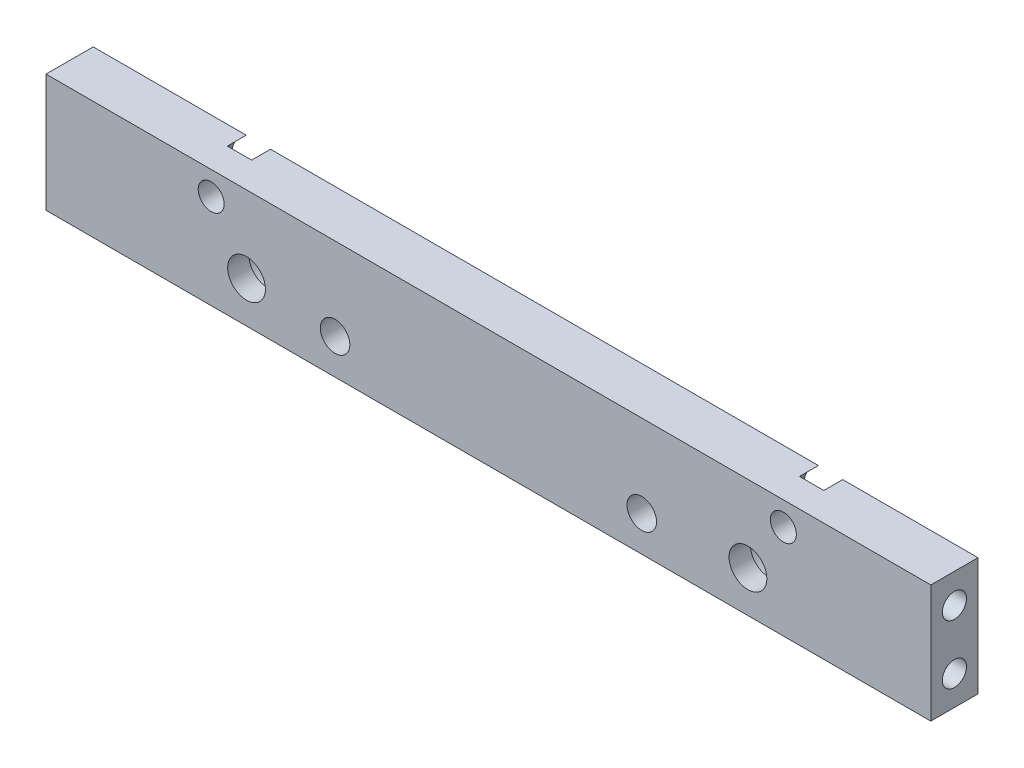
SolidWorks part; units mm, degrees
ref_plane "Front Plane" through (0, 0, 0) normal (0, 0, 1) x (1, 0, 0)
ref_plane "Top Plane" through (0, 0, 0) normal (0, 1, 0) x (1, 0, 0)
ref_plane "Right Plane" through (0, 0, 0) normal (1, 0, 0) x (0, 0, -1)
ref_plane "Plane1" through (0, 0, 4) normal (0, 0, 1) x (1, 0, 0)
sketch "Sketch1" plane through (0, 0, 4) normal (0, 0, 1) x (1, 0, 0)
  line L0 (37.5, -5) -> (37.5, 5)
  line L1 (37.5, 5) -> (-37.5, 5)
  line L2 (-37.5, 5) -> (-37.5, -5)
  line L3 (-37.5, -5) -> (37.5, -5)
extrude "Boss-Extrude1" add sketch "Sketch1" against normal blind 4
hole_wizard "Ø2.5 (2.5) Diameter Hole1" positions "Sketch3" profile "Sketch2" hole size "Ø2.5" standard "ANSI Metric"
sketch "Sketch3" plane through (0, 0, 0) normal (0, 0, -1) x (-1, 0, 0)
  point P0 (-13, -2)
  point P1 (13, -2)
sketch "Sketch2" plane through (13, -2, 0) normal (1, 0, 0) x (0, 1, 0)
  line L0 (0, 0) -> (0, 4)
  line L1 (0, 4) -> (1.25, 4)
  line L2 (1.25, 4) -> (1.25, 0)
  line L5 (1.25, 0) -> (0, 0)
  line L11 (0, -6.35) -> (0, 107.95) construction
  dimension "Thru Hole Dia." = 2.5
  dimension "Thru Hole Depth" = 4
hole_wizard "CBORE for M3 Hex Head Machine Screw1" positions "Sketch5" profile "Sketch4" counterbore size "M3" standard "ANSI Metric"
sketch "Sketch5" plane through (0, 0, 0) normal (0, 0, -1) x (-1, 0, 0)
  point P0 (-22, -1.5)
  point P1 (20.5, -1.5)
sketch "Sketch4" plane through (22, -1.5, 0) normal (1, 0, 0) x (0, 1, 0)
  line L0 (0, 0) -> (0, 4)
  line L1 (0, 4) -> (1.6, 4)
  line L3 (1.6, 4) -> (1.6, 2.2)
  line L4 (1.6, 2.2) -> (2.9, 2.2)
  line L5 (2.9, 2.2) -> (2.9, 0)
  line L7 (2.9, 0) -> (0, 0)
  line L11 (0, -6.35) -> (0, 107.95) construction
  dimension "Thru Hole Dia." = 3.2
  dimension "Thru Hole Depth" = 4
  dimension "C'Bore Dia." = 5.8
  dimension "C'Bore Depth" = 2.2
hole_wizard "CBORE for M2 Hex Head Machine Screw1" positions "Sketch7" profile "Sketch6" counterbore size "M2" standard "ANSI Metric"
sketch "Sketch7" plane through (0, 0, 0) normal (0, 0, -1) x (-1, 0, 0)
  point P0 (23.5, 3)
  point P1 (-25, 3)
sketch "Sketch6" plane through (-23.5, 3, 0) normal (1, 0, 0) x (0, 1, 0)
  line L0 (0, 0) -> (0, 4)
  line L1 (0, 4) -> (1.1, 4)
  line L3 (1.1, 4) -> (1.1, 1.6)
  line L4 (1.1, 1.6) -> (2.25, 1.6)
  line L5 (2.25, 1.6) -> (2.25, 0)
  line L7 (2.25, 0) -> (0, 0)
  line L11 (0, -6.35) -> (0, 107.95) construction
  dimension "Thru Hole Dia." = 2.2
  dimension "Thru Hole Depth" = 4
  dimension "C'Bore Dia." = 4.5
  dimension "C'Bore Depth" = 1.6
hole_wizard "Ø2.05 (2.05) Diameter Hole1" positions "Sketch9" profile "Sketch8" hole size "Ø2.05" standard "ANSI Metric"
sketch "Sketch9" plane through (37.5, 0, 0) normal (1, 0, 0) x (0, 0, -1)
  point P0 (-2, 2.5)
  point P1 (-2, -2.5)
sketch "Sketch8" plane through (37.5, 2.5, 2) normal (0, 1, 0) x (0, 0, -1)
  line L0 (0, 0) -> (0, 8.6159)
  line L1 (0, 8.6159) -> (1.025, 8)
  line L2 (1.025, 8) -> (1.025, 0)
  line L5 (1.025, 0) -> (0, 0)
  line L10 (0, 8.6159) -> (-1.025, 8) construction
  line L11 (0, -6.35) -> (0, 107.95) construction
  dimension "Hole Dia." = 2.05
  dimension "Hole Depth" = 8
  dimension "Drill Angle" = 118
hole_wizard "Ø2.05 (2.05) Diameter Hole2" positions "Sketch11" profile "Sketch10" hole size "Ø2.05" standard "ANSI Metric"
sketch "Sketch11" plane through (-37.5, 0, 0) normal (-1, 0, 0) x (0, 0, 1)
  point P0 (2, -2.5)
  point P1 (2, 2.5)
sketch "Sketch10" plane through (-37.5, -2.5, 2) normal (0, 1, 0) x (0, 0, 1)
  line L0 (0, 0) -> (0, 8.6159)
  line L1 (0, 8.6159) -> (1.025, 8)
  line L2 (1.025, 8) -> (1.025, 0)
  line L5 (1.025, 0) -> (0, 0)
  line L10 (0, 8.6159) -> (-1.025, 8) construction
  line L11 (0, -6.35) -> (0, 107.95) construction
  dimension "Hole Dia." = 2.05
  dimension "Hole Depth" = 8
  dimension "Drill Angle" = 118
